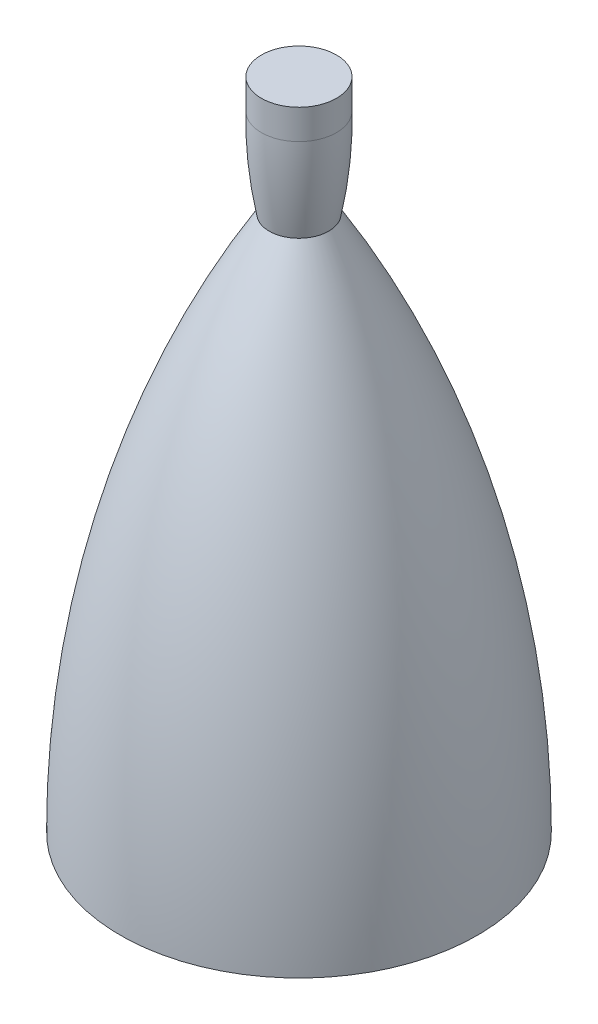
SolidWorks part; units mm, degrees
ref_plane "Front Plane" through (0, 0, 0) normal (0, 0, 1) x (1, 0, 0)
ref_plane "Top Plane" through (0, 0, 0) normal (0, 1, 0) x (1, 0, 0)
ref_plane "Right Plane" through (0, 0, 0) normal (1, 0, 0) x (0, 0, -1)
sketch "Sketch1" plane through (0, 0, 0) normal (0, 0, 1) x (1, 0, 0)
  line L0 (0, 0) -> (152.4, 0)
  line L1 (0, 0) -> (0, 457.2)
  line L2 (0, 457.2) -> (25.4, 457.2) construction
  line L3 (0, 457.2) -> (0, 533.4)
  line L7 (0, 533.4) -> (0, 558.8)
  line L8 (0, 558.8) -> (32.0596, 558.8)
  line L9 (32.0596, 533.4) -> (32.0596, 558.8)
  arc A0 (25.4, 457.2) -> (152.4, 0) centre (-731.9899, 0.575) cw
  arc A1 (25.4, 457.2) -> (32.0596, 533.4) centre (-337.1114, 527.2734) ccw
  dimension "D1" = 152.4
  dimension "D2" = 457.2
  dimension "D3" = 25.4
  dimension "D4" = 76.2
  dimension "D5" = 76.2
  dimension "D6" = 25.4
revolve "Revolve1" add sketch "Sketch1" angle 360 about L1
